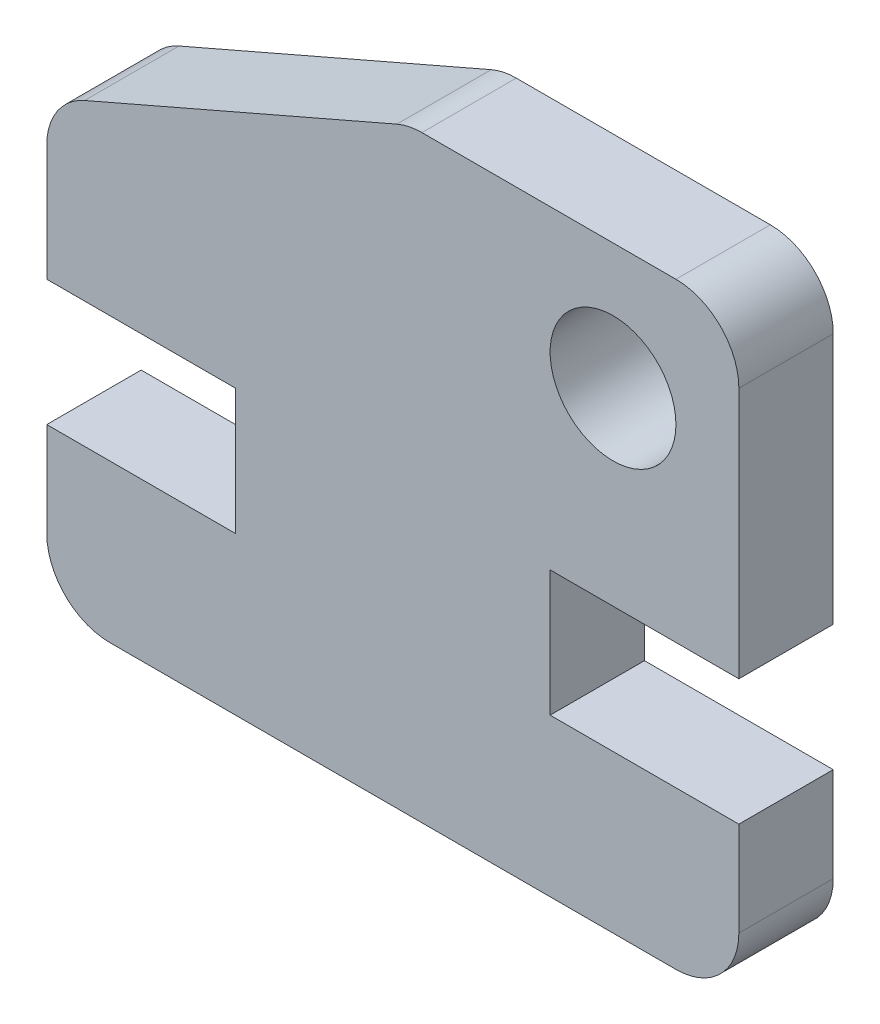
SolidWorks part; units mm, degrees
ref_plane "Ebene vorne" through (0, 0, 0) normal (0, 0, 1) x (1, 0, 0)
ref_plane "Ebene oben" through (0, 0, 0) normal (0, 1, 0) x (1, 0, 0)
ref_plane "Ebene rechts" through (0, 0, 0) normal (1, 0, 0) x (0, 0, -1)
sketch "Skizze1" plane through (0, 0, 0) normal (0, 0, 1) x (1, 0, 0)
  line L0 (0, 0) -> (0, 19) construction
  line L1 (-11, 5) -> (-11, 0)
  line L2 (-11, 19) -> (11, 19)
  line L3 (-11, 19) -> (-11, 9)
  line L4 (-11, 0) -> (11, 0)
  line L5 (5, 5) -> (11, 5)
  line L6 (-11, 19) -> (0, 5) construction
  line L7 (-11, 0) -> (0, 5) construction
  line L8 (-5, 9) -> (-11, 9)
  line L9 (-5, 9) -> (-5, 5)
  line L10 (-5, 5) -> (-11, 5)
  line L11 (5, 9) -> (5, 5)
  line L12 (-5, 9) -> (-11, 7) construction
  line L13 (-5, 5) -> (-11, 7) construction
  line L14 (5, 9) -> (11, 9)
  line L15 (11, 19) -> (11, 9)
  line L16 (11, 5) -> (11, 0)
  line L17 (-11, 7) -> (11, 7) construction
  point P7 (-11, 7)
  point P8 (11, 7)
  dimension "D1" = 10
  dimension "D2" = 10
  dimension "D3" = 22
  dimension "D4" = 4
  dimension "D5" = 5
extrude "Aufsatz-Linear austragen1" add sketch "Skizze1" along normal blind 3
hole_wizard "Ø4.0 (4) Durchmesser Bohrung1" positions "Skizze3" profile "Skizze2" hole size "Ø4.0" standard "DIN" end condition through all
sketch "Skizze3" plane through (0, 0, 3) normal (0, 0, 1) x (1, 0, 0)
  line L0 (11, 15) -> (3.5397, 15) construction
  line L1 (11, 9) -> (11, 19) construction
  line L2 (11, 19) -> (-11, 19) construction
  point P0 (7, 15)
  dimension "D1" = 4
  dimension "D2" = 4
sketch "Skizze2" plane through (7, 15, 3) normal (1, 0, 0) x (0, -1, 0)
  line L0 (0, 0) -> (0, 3)
  line L1 (0, 3) -> (2, 3)
  line L2 (2, 3) -> (2, 0)
  line L5 (2, 0) -> (0, 0)
  line L11 (0, -6.35) -> (0, 107.95) construction
  dimension "Bohrerdurchmesser" = 4
  dimension "Bohrungstiefe" = 3
sketch "Skizze4" plane through (0, 0, 3) normal (0, 0, 1) x (1, 0, 0)
  line L0 (-11, 14) -> (0.5094, 19)
  line L1 (-11, 19) -> (-11, 9) construction
  line L2 (11, 19) -> (-11, 19) construction
  line L3 (0.5094, 19) -> (-11, 19)
  line L4 (-11, 19) -> (-11, 14)
extrude "Schnitt-Linear austragen1" cut sketch "Skizze4" against normal blind 3
fillet "Verrundung2" radius 2 5 edges at (0.5094, 19, 1.5) (-11, 14, 1.5) (-11, 0, 1.5) (11, 0, 1.5) (11, 19, 1.5)
